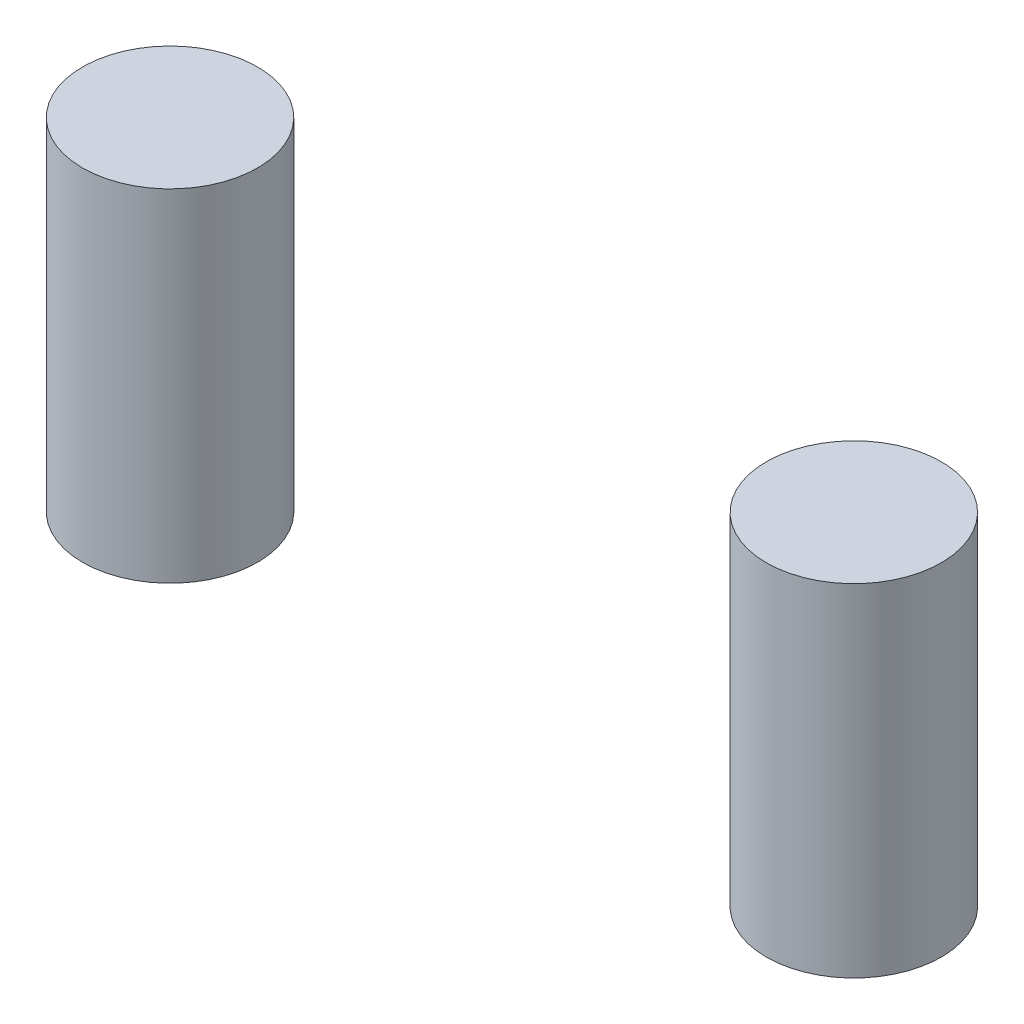
SolidWorks part; units mm, degrees
ref_plane "Front Plane" through (0, 0, 0) normal (0, 0, 1) x (1, 0, 0)
ref_plane "Top Plane" through (0, 0, 0) normal (0, 1, 0) x (1, 0, 0)
ref_plane "Right Plane" through (0, 0, 0) normal (1, 0, 0) x (0, 0, -1)
sketch "Sketch1" plane through (0, 0, 0) normal (0, 1, 0) x (1, 0, 0)
  circle A0 centre (3.1, -3.1) radius 3.075
  circle A1 centre (27.125, -3.1) radius 3.075
  dimension "D1" = 6.15
  dimension "D2" = 6.15
extrude "Boss-Extrude1" add sketch "Sketch1" along normal blind 12
